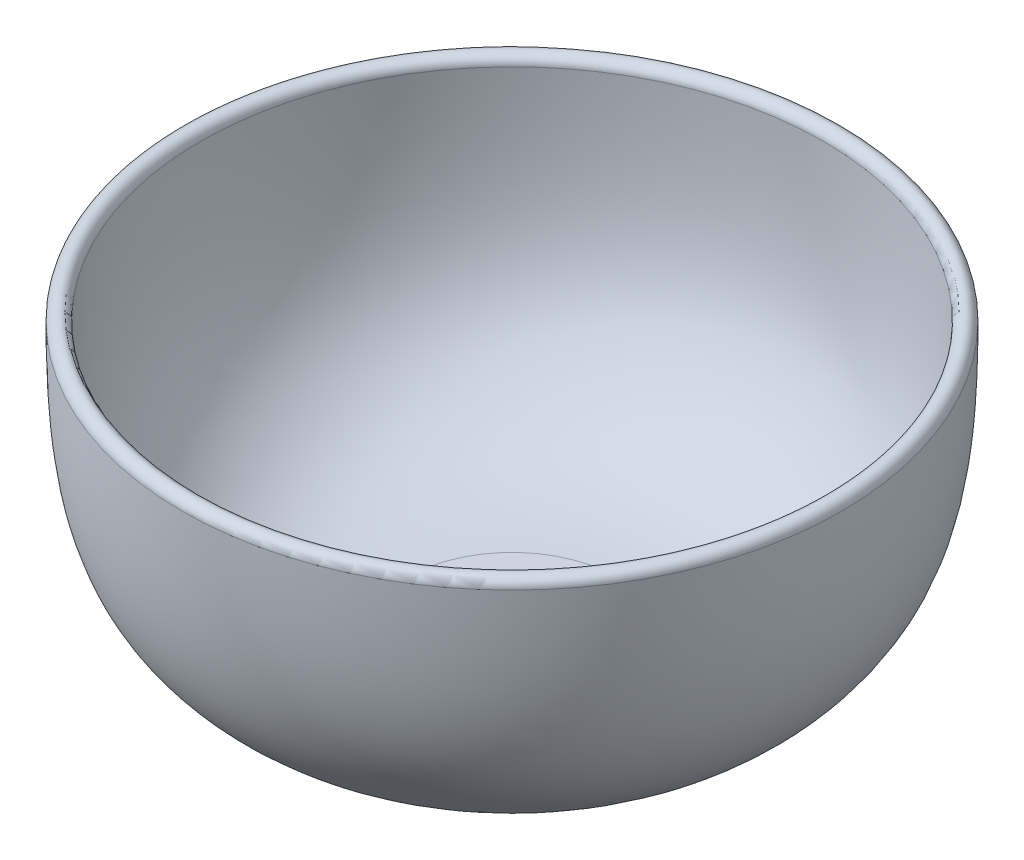
SolidWorks part; units mm, degrees
ref_plane "Front Plane" through (0, 0, 0) normal (0, 0, 1) x (1, 0, 0)
ref_plane "Top Plane" through (0, 0, 0) normal (0, 1, 0) x (1, 0, 0)
ref_plane "Right Plane" through (0, 0, 0) normal (1, 0, 0) x (0, 0, -1)
sketch "Sketch1" plane through (0, 0, 0) normal (0, 0, 1) x (1, 0, 0)
  line L8 (0, -40) -> (-30, -40) construction
  line L9 (-90, 121.3656) -> (-90, 21.7207) construction
  line L10 (0, -40) -> (0, 40) construction
  line L11 (0, -37.46) -> (-30, -37.46)
  line L12 (0, -42.54) -> (-30, -42.54)
  line L13 (0, -37.46) -> (0, -42.54)
  arc A1 (-87.46, 40) -> (-92.54, 40) centre (-90, 40) ccw
  spline S0 degree 3 poles (-30, -40) (-52.1034, -40) (-84.2775, -20.7457) (-90, 7.1036) (-90, 40) knots 0 0 0 0 0.383542 1 1 1 1 construction
  spline S1 degree 1 poles (-30, -37.46) (-87.46, 40) knots 0 0 1 1 construction
  spline S2 degree 3 poles (-30, -37.46) (-30.861, -37.46) (-32.6064, -37.4361) (-35.9079, -37.2964) (-39.8178, -36.9561) (-44.1416, -36.3045) (-49.4591, -35.1394) (-55.3145, -33.1804) (-61.2603, -30.1809) (-66.3061, -26.6749) (-70.628, -22.7788) (-74.3605, -18.6632) (-78.5537, -12.8922) (-81.7205, -6.4638) (-84.0381, 1.0119) (-85.3835, 7.2338) (-86.3679, 14.1523) (-86.9149, 20.5612) (-87.2061, 26.1118) (-87.3559, 30.4938) (-87.4276, 34.3413) (-87.4555, 37.5284) (-87.46, 39.1811) (-87.46, 40) knots 0 0 0 0 0.015625 0.03125 0.0625 0.09375 0.125 0.1875 0.25 0.3125 0.375 0.4375 0.5 0.625 0.6875 0.75 0.8125 0.875 0.90625 0.9375 0.96875 0.984375 1 1 1 1
  spline S3 degree 1 poles (-30, -42.54) (-92.54, 40) knots 0 0 1 1 construction
  spline S4 degree 3 poles (-30, -42.54) (-30.908, -42.54) (-32.746, -42.5149) (-36.2429, -42.367) (-40.4084, -42.005) (-45.0564, -41.3052) (-50.8228, -40.0427) (-57.257, -37.8938) (-63.8632, -34.5636) (-69.4784, -30.6599) (-74.2279, -26.3753) (-78.2971, -21.889) (-82.9532, -15.4878) (-86.4581, -8.3535) (-88.9634, -0.2579) (-90.3921, 6.3596) (-91.4201, 13.5974) (-91.9837, 20.212) (-92.2817, 25.8955) (-92.4344, 30.3628) (-92.5072, 34.2704) (-92.5354, 37.5001) (-92.54, 39.1714) (-92.54, 40) knots 0 0 0 0 0.015625 0.03125 0.0625 0.09375 0.125 0.1875 0.25 0.3125 0.375 0.4375 0.5 0.625 0.6875 0.75 0.8125 0.875 0.90625 0.9375 0.96875 0.984375 1 1 1 1
  point P5 (0, 0)
  dimension "D1" = 90
  dimension "D2" = 80
  dimension "D5" = 30
  dimension "D3" = 2.54
  dimension "D4" = 2.54
revolve "Revolve1" add sketch "Sketch1" angle 360 about L10
